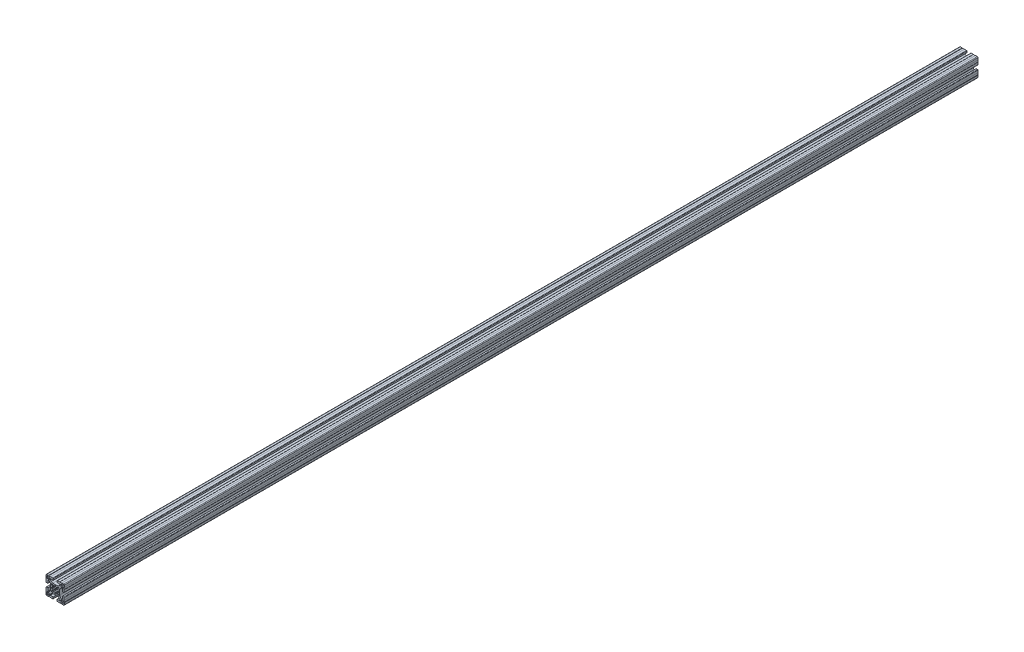
SolidWorks part; units mm, degrees
ref_plane "Plano frontal" through (0, 0, 0) normal (0, 0, 1) x (1, 0, 0)
ref_plane "Plano superior" through (0, 0, 0) normal (0, 1, 0) x (1, 0, 0)
ref_plane "Plano direito" through (0, 0, 0) normal (1, 0, 0) x (0, 0, -1)
sketch "Esboço1" plane through (0, 0, 0) normal (0, 0, 1) x (1, 0, 0)
  point P0 (0, 0)
  line B0 (-17.8572, 16.7966) -> (-17.4167, 16.356)
  arc B1 (-16.7966, 17.8572) -> (-17.8572, 16.7966) centre (-17.3269, 17.3269) ccw
  line B2 (-16.356, 17.4167) -> (-16.7966, 17.8572)
  arc B3 (-14.044, 17.4167) -> (-16.356, 17.4167) centre (-15.2, 15.2) ccw
  line B4 (-13.6034, 17.8572) -> (-14.044, 17.4167)
  arc B5 (-12.5428, 16.7966) -> (-13.6034, 17.8572) centre (-13.0731, 17.3269) ccw
  line B6 (-12.9833, 16.356) -> (-12.5428, 16.7966)
  arc B7 (-12.9833, 14.044) -> (-12.9833, 16.356) centre (-15.2, 15.2) ccw
  line B8 (-12.5428, 13.6034) -> (-12.9833, 14.044)
  arc B9 (-13.6034, 12.5428) -> (-12.5428, 13.6034) centre (-13.0731, 13.0731) ccw
  line B10 (-14.044, 12.9833) -> (-13.6034, 12.5428)
  arc B11 (-16.356, 12.9833) -> (-14.044, 12.9833) centre (-15.2, 15.2) ccw
  line B12 (-16.7966, 12.5428) -> (-16.356, 12.9833)
  arc B13 (-17.8572, 13.6034) -> (-16.7966, 12.5428) centre (-17.3269, 13.0731) ccw
  line B14 (-17.4167, 14.044) -> (-17.8572, 13.6034)
  arc B15 (-17.4167, 16.356) -> (-17.4167, 14.044) centre (-15.2, 15.2) ccw
  line B16 (17.4167, 14.044) -> (17.8572, 13.6034)
  arc B17 (16.7966, 12.5428) -> (17.8572, 13.6034) centre (17.3269, 13.0731) ccw
  line B18 (16.7966, 12.5428) -> (16.356, 12.9833)
  arc B19 (14.044, 12.9833) -> (16.356, 12.9833) centre (15.2, 15.2) ccw
  line B20 (14.044, 12.9833) -> (13.6034, 12.5428)
  arc B21 (12.5428, 13.6034) -> (13.6034, 12.5428) centre (13.0731, 13.0731) ccw
  line B22 (12.5428, 13.6034) -> (12.9833, 14.044)
  arc B23 (12.9833, 16.356) -> (12.9833, 14.044) centre (15.2, 15.2) ccw
  line B24 (12.9833, 16.356) -> (12.5428, 16.7966)
  arc B25 (13.6034, 17.8572) -> (12.5428, 16.7966) centre (13.0731, 17.3269) ccw
  line B26 (13.6034, 17.8572) -> (14.044, 17.4167)
  arc B27 (16.356, 17.4167) -> (14.044, 17.4167) centre (15.2, 15.2) ccw
  line B28 (16.356, 17.4167) -> (16.7966, 17.8572)
  arc B29 (17.8572, 16.7966) -> (16.7966, 17.8572) centre (17.3269, 17.3269) ccw
  line B30 (17.8572, 16.7966) -> (17.4167, 16.356)
  arc B31 (17.4167, 14.044) -> (17.4167, 16.356) centre (15.2, 15.2) ccw
  line B32 (-17.4167, -14.044) -> (-17.8572, -13.6034)
  arc B33 (-16.7966, -12.5428) -> (-17.8572, -13.6034) centre (-17.3269, -13.0731) ccw
  line B34 (-16.7966, -12.5428) -> (-16.356, -12.9833)
  arc B35 (-14.044, -12.9833) -> (-16.356, -12.9833) centre (-15.2, -15.2) ccw
  line B36 (-14.044, -12.9833) -> (-13.6034, -12.5428)
  arc B37 (-12.5428, -13.6034) -> (-13.6034, -12.5428) centre (-13.0731, -13.0731) ccw
  line B38 (-12.5428, -13.6034) -> (-12.9833, -14.044)
  arc B39 (-12.9833, -16.356) -> (-12.9833, -14.044) centre (-15.2, -15.2) ccw
  line B40 (-12.9833, -16.356) -> (-12.5428, -16.7966)
  arc B41 (-13.6034, -17.8572) -> (-12.5428, -16.7966) centre (-13.0731, -17.3269) ccw
  line B42 (-13.6034, -17.8572) -> (-14.044, -17.4167)
  arc B43 (-16.356, -17.4167) -> (-14.044, -17.4167) centre (-15.2, -15.2) ccw
  line B44 (-16.356, -17.4167) -> (-16.7966, -17.8572)
  arc B45 (-17.8572, -16.7966) -> (-16.7966, -17.8572) centre (-17.3269, -17.3269) ccw
  line B46 (-17.8572, -16.7966) -> (-17.4167, -16.356)
  arc B47 (-17.4167, -14.044) -> (-17.4167, -16.356) centre (-15.2, -15.2) ccw
  line B48 (17.8572, -16.7966) -> (17.4167, -16.356)
  arc B49 (16.7966, -17.8572) -> (17.8572, -16.7966) centre (17.3269, -17.3269) ccw
  line B50 (16.356, -17.4167) -> (16.7966, -17.8572)
  arc B51 (14.044, -17.4167) -> (16.356, -17.4167) centre (15.2, -15.2) ccw
  line B52 (13.6034, -17.8572) -> (14.044, -17.4167)
  arc B53 (12.5428, -16.7966) -> (13.6034, -17.8572) centre (13.0731, -17.3269) ccw
  line B54 (12.9833, -16.356) -> (12.5428, -16.7966)
  arc B55 (12.9833, -14.044) -> (12.9833, -16.356) centre (15.2, -15.2) ccw
  line B56 (12.5428, -13.6034) -> (12.9833, -14.044)
  arc B57 (13.6034, -12.5428) -> (12.5428, -13.6034) centre (13.0731, -13.0731) ccw
  line B58 (14.044, -12.9833) -> (13.6034, -12.5428)
  arc B59 (16.356, -12.9833) -> (14.044, -12.9833) centre (15.2, -15.2) ccw
  line B60 (16.7966, -12.5428) -> (16.356, -12.9833)
  arc B61 (17.8572, -13.6034) -> (16.7966, -12.5428) centre (17.3269, -13.0731) ccw
  line B62 (17.4167, -14.044) -> (17.8572, -13.6034)
  arc B63 (17.4167, -16.356) -> (17.4167, -14.044) centre (15.2, -15.2) ccw
  line B64 (4.15, -18.8) -> (4.15, -15.9)
  arc B65 (4.25, -15.8) -> (4.15, -15.9) centre (4.25, -15.9) ccw
  line B66 (4.25, -15.8) -> (10.5, -15.8)
  arc B67 (10.5, -15.8) -> (11, -15.3) centre (10.5, -15.3) ccw
  line B68 (11, -15.3) -> (11, -14.4497)
  arc B69 (11, -14.4497) -> (10.5607, -13.3891) centre (9.5, -14.4497) ccw
  line B70 (10.5607, -13.3891) -> (8.636, -11.4645)
  arc B71 (8.636, -11.4645) -> (5.1005, -10) centre (5.1005, -15) ccw
  line B72 (5.1005, -10) -> (0, -10)
  line B73 (0, -10) -> (-5.1005, -10)
  arc B74 (-5.1005, -10) -> (-8.636, -11.4645) centre (-5.1005, -15) ccw
  line B75 (-8.636, -11.4645) -> (-10.5607, -13.3891)
  arc B76 (-10.5607, -13.3891) -> (-11, -14.4497) centre (-9.5, -14.4497) ccw
  line B77 (-11, -14.4497) -> (-11, -15.3)
  arc B78 (-11, -15.3) -> (-10.5, -15.8) centre (-10.5, -15.3) ccw
  line B79 (-10.5, -15.8) -> (-4.25, -15.8)
  arc B80 (-4.15, -15.9) -> (-4.25, -15.8) centre (-4.25, -15.9) ccw
  line B81 (-4.15, -15.9) -> (-4.15, -18.8)
  arc B82 (-5.15, -19.8) -> (-4.15, -18.8) centre (-5.15, -18.8) ccw
  line B83 (-5.15, -19.8) -> (-9.8, -19.8)
  line B84 (-9.8, -19.8) -> (-10, -19.6)
  line B85 (-10, -19.6) -> (-14, -19.6)
  line B86 (-14, -19.6) -> (-14.4, -20)
  line B87 (-14.4, -20) -> (-18.5, -20)
  arc B88 (-20, -18.5) -> (-18.5, -20) centre (-18.5, -18.5) ccw
  line B89 (-20, -18.5) -> (-20, -14.4)
  line B90 (-20, -14.4) -> (-19.6, -14)
  line B91 (-19.6, -14) -> (-19.6, -10)
  line B92 (-19.6, -10) -> (-19.8, -9.8)
  line B93 (-19.8, -9.8) -> (-19.8, -5.15)
  arc B94 (-18.8, -4.15) -> (-19.8, -5.15) centre (-18.8, -5.15) ccw
  line B95 (-18.8, -4.15) -> (-15.9, -4.15)
  arc B96 (-15.8, -4.25) -> (-15.9, -4.15) centre (-15.9, -4.25) ccw
  line B97 (-15.8, -4.25) -> (-15.8, -10.5)
  arc B98 (-15.8, -10.5) -> (-15.3, -11) centre (-15.3, -10.5) ccw
  line B99 (-15.3, -11) -> (-14.4497, -11)
  arc B100 (-14.4497, -11) -> (-13.3891, -10.5607) centre (-14.4497, -9.5) ccw
  line B101 (-13.3891, -10.5607) -> (-11.4645, -8.636)
  arc B102 (-11.4645, -8.636) -> (-10, -5.1005) centre (-15, -5.1005) ccw
  line B103 (-10, -5.1005) -> (-10, 0)
  line B104 (-10, 0) -> (-10, 5.1005)
  arc B105 (-10, 5.1005) -> (-11.4645, 8.636) centre (-15, 5.1005) ccw
  line B106 (-11.4645, 8.636) -> (-13.3891, 10.5607)
  arc B107 (-13.3891, 10.5607) -> (-14.4497, 11) centre (-14.4497, 9.5) ccw
  line B108 (-14.4497, 11) -> (-15.3, 11)
  arc B109 (-15.3, 11) -> (-15.8, 10.5) centre (-15.3, 10.5) ccw
  line B110 (-15.8, 10.5) -> (-15.8, 4.25)
  arc B111 (-15.9, 4.15) -> (-15.8, 4.25) centre (-15.9, 4.25) ccw
  line B112 (-15.9, 4.15) -> (-18.8, 4.15)
  arc B113 (-19.8, 5.15) -> (-18.8, 4.15) centre (-18.8, 5.15) ccw
  line B114 (-19.8, 5.15) -> (-19.8, 9.8)
  line B115 (-19.8, 9.8) -> (-19.6, 10)
  line B116 (-19.6, 10) -> (-19.6, 14)
  line B117 (-19.6, 14) -> (-20, 14.4)
  line B118 (-20, 14.4) -> (-20, 18.5)
  arc B119 (-18.5, 20) -> (-20, 18.5) centre (-18.5, 18.5) ccw
  line B120 (-18.5, 20) -> (-14.4, 20)
  line B121 (-14.4, 20) -> (-14, 19.6)
  line B122 (-14, 19.6) -> (-10, 19.6)
  line B123 (-10, 19.6) -> (-9.8, 19.8)
  line B124 (-9.8, 19.8) -> (-5.15, 19.8)
  arc B125 (-4.15, 18.8) -> (-5.15, 19.8) centre (-5.15, 18.8) ccw
  line B126 (-4.15, 18.8) -> (-4.15, 15.9)
  arc B127 (-4.25, 15.8) -> (-4.15, 15.9) centre (-4.25, 15.9) ccw
  line B128 (-4.25, 15.8) -> (-10.5, 15.8)
  arc B129 (-10.5, 15.8) -> (-11, 15.3) centre (-10.5, 15.3) ccw
  line B130 (-11, 15.3) -> (-11, 14.4497)
  arc B131 (-11, 14.4497) -> (-10.5607, 13.3891) centre (-9.5, 14.4497) ccw
  line B132 (-10.5607, 13.3891) -> (-8.636, 11.4645)
  arc B133 (-8.636, 11.4645) -> (-5.1005, 10) centre (-5.1005, 15) ccw
  line B134 (-5.1005, 10) -> (0, 10)
  line B135 (0, 10) -> (5.1005, 10)
  arc B136 (5.1005, 10) -> (8.636, 11.4645) centre (5.1005, 15) ccw
  line B137 (8.636, 11.4645) -> (10.5607, 13.3891)
  arc B138 (10.5607, 13.3891) -> (11, 14.4497) centre (9.5, 14.4497) ccw
  line B139 (11, 14.4497) -> (11, 15.3)
  arc B140 (11, 15.3) -> (10.5, 15.8) centre (10.5, 15.3) ccw
  line B141 (10.5, 15.8) -> (4.25, 15.8)
  arc B142 (4.15, 15.9) -> (4.25, 15.8) centre (4.25, 15.9) ccw
  line B143 (4.15, 15.9) -> (4.15, 18.8)
  arc B144 (5.15, 19.8) -> (4.15, 18.8) centre (5.15, 18.8) ccw
  line B145 (5.15, 19.8) -> (9.8, 19.8)
  line B146 (9.8, 19.8) -> (10, 19.6)
  line B147 (10, 19.6) -> (14, 19.6)
  line B148 (14, 19.6) -> (14.4, 20)
  line B149 (14.4, 20) -> (18.5, 20)
  arc B150 (20, 18.5) -> (18.5, 20) centre (18.5, 18.5) ccw
  line B151 (20, 18.5) -> (20, 14.4)
  line B152 (20, 14.4) -> (19.6, 14)
  line B153 (19.6, 14) -> (19.6, 10)
  line B154 (19.6, 10) -> (19.8, 9.8)
  line B155 (19.8, 9.8) -> (19.8, 5.15)
  arc B156 (18.8, 4.15) -> (19.8, 5.15) centre (18.8, 5.15) ccw
  line B157 (18.8, 4.15) -> (15.9, 4.15)
  arc B158 (15.8, 4.25) -> (15.9, 4.15) centre (15.9, 4.25) ccw
  line B159 (15.8, 4.25) -> (15.8, 10.5)
  arc B160 (15.8, 10.5) -> (15.3, 11) centre (15.3, 10.5) ccw
  line B161 (15.3, 11) -> (14.4497, 11)
  arc B162 (14.4497, 11) -> (13.3891, 10.5607) centre (14.4497, 9.5) ccw
  line B163 (13.3891, 10.5607) -> (11.4645, 8.636)
  arc B164 (11.4645, 8.636) -> (10, 5.1005) centre (15, 5.1005) ccw
  line B165 (10, 5.1005) -> (10, 0)
  line B166 (10, 0) -> (10, -5.1005)
  arc B167 (10, -5.1005) -> (11.4645, -8.636) centre (15, -5.1005) ccw
  line B168 (11.4645, -8.636) -> (13.3891, -10.5607)
  arc B169 (13.3891, -10.5607) -> (14.4497, -11) centre (14.4497, -9.5) ccw
  line B170 (14.4497, -11) -> (15.3, -11)
  arc B171 (15.3, -11) -> (15.8, -10.5) centre (15.3, -10.5) ccw
  line B172 (15.8, -10.5) -> (15.8, -4.25)
  arc B173 (15.9, -4.15) -> (15.8, -4.25) centre (15.9, -4.25) ccw
  line B174 (15.9, -4.15) -> (18.8, -4.15)
  arc B175 (19.8, -5.15) -> (18.8, -4.15) centre (18.8, -5.15) ccw
  line B176 (19.8, -5.15) -> (19.8, -9.8)
  line B177 (19.8, -9.8) -> (19.6, -10)
  line B178 (19.6, -10) -> (19.6, -14)
  line B179 (19.6, -14) -> (20, -14.4)
  line B180 (20, -14.4) -> (20, -18.5)
  arc B181 (18.5, -20) -> (20, -18.5) centre (18.5, -18.5) ccw
  line B182 (18.5, -20) -> (14.4, -20)
  line B183 (14.4, -20) -> (14, -19.6)
  line B184 (14, -19.6) -> (10, -19.6)
  line B185 (10, -19.6) -> (9.8, -19.8)
  line B186 (9.8, -19.8) -> (5.15, -19.8)
  arc B187 (4.15, -18.8) -> (5.15, -19.8) centre (5.15, -18.8) ccw
  line B188 (-5.3139, -7.6355) -> (-7.6488, -8.2611)
  arc B189 (-8.2611, -7.6488) -> (-7.6488, -8.2611) centre (-7.7782, -7.7782) ccw
  line B190 (-8.2611, -7.6488) -> (-7.6355, -5.3139)
  arc B191 (-7.4569, -5.0466) -> (-7.6355, -5.3139) centre (-7.1525, -5.4433) ccw
  line B192 (-7.4569, -5.0466) -> (-5.744, -3.7322)
  arc B193 (-6.7007, -1.4225) -> (-5.744, -3.7322) centre (0, 0) ccw
  line B194 (-6.7007, -1.4225) -> (-7.5204, -1.3146)
  arc B195 (-7.9522, -0.8735) -> (-7.5204, -1.3146) centre (-7.4552, -0.8189) ccw
  arc B196 (-7.9522, 0.8735) -> (-7.9522, -0.8735) centre (0, 0) ccw
  arc B197 (-7.5204, 1.3146) -> (-7.9522, 0.8735) centre (-7.4552, 0.8189) ccw
  line B198 (-7.5204, 1.3146) -> (-6.7007, 1.4225)
  arc B199 (-5.744, 3.7322) -> (-6.7007, 1.4225) centre (0, 0) ccw
  line B200 (-5.744, 3.7322) -> (-7.4569, 5.0466)
  arc B201 (-7.6355, 5.3139) -> (-7.4569, 5.0466) centre (-7.1525, 5.4433) ccw
  line B202 (-7.6355, 5.3139) -> (-8.2611, 7.6488)
  arc B203 (-7.6488, 8.2611) -> (-8.2611, 7.6488) centre (-7.7782, 7.7782) ccw
  line B204 (-7.6488, 8.2611) -> (-5.3139, 7.6355)
  arc B205 (-5.0466, 7.4569) -> (-5.3139, 7.6355) centre (-5.4433, 7.1525) ccw
  line B206 (-5.0466, 7.4569) -> (-3.7322, 5.744)
  arc B207 (-1.4225, 6.7007) -> (-3.7322, 5.744) centre (0, 0) ccw
  line B208 (-1.4225, 6.7007) -> (-1.3146, 7.5204)
  arc B209 (-0.8735, 7.9522) -> (-1.3146, 7.5204) centre (-0.8189, 7.4552) ccw
  arc B210 (0.8735, 7.9522) -> (-0.8735, 7.9522) centre (0, 0) ccw
  arc B211 (1.3146, 7.5204) -> (0.8735, 7.9522) centre (0.8189, 7.4552) ccw
  line B212 (1.3146, 7.5204) -> (1.4225, 6.7007)
  arc B213 (3.7322, 5.744) -> (1.4225, 6.7007) centre (0, 0) ccw
  line B214 (3.7322, 5.744) -> (5.0466, 7.4569)
  arc B215 (5.3139, 7.6355) -> (5.0466, 7.4569) centre (5.4433, 7.1525) ccw
  line B216 (5.3139, 7.6355) -> (7.6488, 8.2611)
  arc B217 (8.2611, 7.6488) -> (7.6488, 8.2611) centre (7.7782, 7.7782) ccw
  line B218 (8.2611, 7.6488) -> (7.6355, 5.3139)
  arc B219 (7.4569, 5.0466) -> (7.6355, 5.3139) centre (7.1525, 5.4433) ccw
  line B220 (7.4569, 5.0466) -> (5.744, 3.7322)
  arc B221 (6.7007, 1.4225) -> (5.744, 3.7322) centre (0, 0) ccw
  line B222 (6.7007, 1.4225) -> (7.5204, 1.3146)
  arc B223 (7.9522, 0.8735) -> (7.5204, 1.3146) centre (7.4552, 0.8189) ccw
  arc B224 (7.9522, -0.8735) -> (7.9522, 0.8735) centre (0, 0) ccw
  arc B225 (7.5204, -1.3146) -> (7.9522, -0.8735) centre (7.4552, -0.8189) ccw
  line B226 (7.5204, -1.3146) -> (6.7007, -1.4225)
  arc B227 (5.744, -3.7322) -> (6.7007, -1.4225) centre (0, 0) ccw
  line B228 (5.744, -3.7322) -> (7.4569, -5.0466)
  arc B229 (7.6355, -5.3139) -> (7.4569, -5.0466) centre (7.1525, -5.4433) ccw
  line B230 (7.6355, -5.3139) -> (8.2611, -7.6488)
  arc B231 (7.6488, -8.2611) -> (8.2611, -7.6488) centre (7.7782, -7.7782) ccw
  line B232 (7.6488, -8.2611) -> (5.3139, -7.6355)
  arc B233 (5.0466, -7.4569) -> (5.3139, -7.6355) centre (5.4433, -7.1525) ccw
  line B234 (5.0466, -7.4569) -> (3.7322, -5.744)
  arc B235 (1.4225, -6.7007) -> (3.7322, -5.744) centre (0, 0) ccw
  line B236 (1.4225, -6.7007) -> (1.3146, -7.5204)
  arc B237 (0.8735, -7.9522) -> (1.3146, -7.5204) centre (0.8189, -7.4552) ccw
  arc B238 (-0.8735, -7.9522) -> (0.8735, -7.9522) centre (0, 0) ccw
  arc B239 (-1.3146, -7.5204) -> (-0.8735, -7.9522) centre (-0.8189, -7.4552) ccw
  line B240 (-1.3146, -7.5204) -> (-1.4225, -6.7007)
  arc B241 (-3.7322, -5.744) -> (-1.4225, -6.7007) centre (0, 0) ccw
  line B242 (-3.7322, -5.744) -> (-5.0466, -7.4569)
  arc B243 (-5.3139, -7.6355) -> (-5.0466, -7.4569) centre (-5.4433, -7.1525) ccw
sketch_block_instance "P40103-1"
sketch_block "P40103"
other "Item de detalhe3"
other "Item de detalhe4"
extrude "Ressalto-extrusão1" add sketch "Esboço1" along normal mid plane 2000
